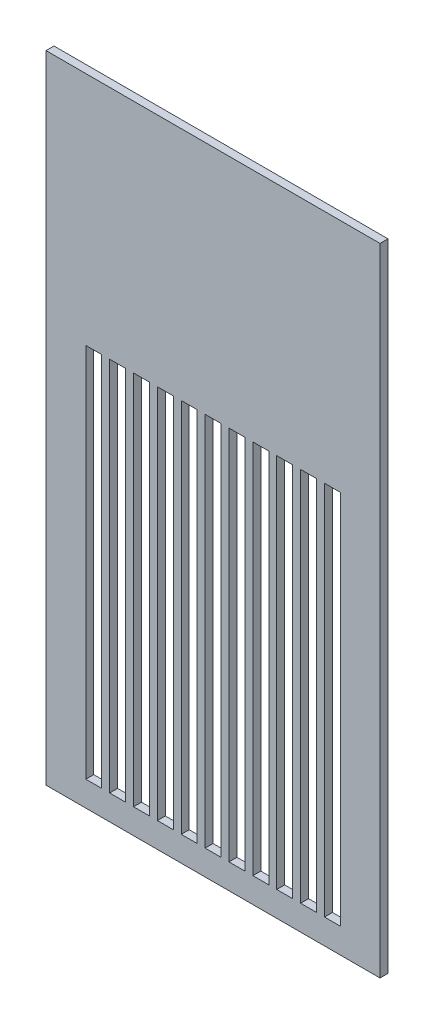
SolidWorks part; units mm, degrees
ref_plane "Front Plane" through (0, 0, 0) normal (0, 0, 1) x (1, 0, 0)
ref_plane "Top Plane" through (0, 0, 0) normal (0, 1, 0) x (1, 0, 0)
ref_plane "Right Plane" through (0, 0, 0) normal (1, 0, 0) x (0, 0, -1)
sketch "Sketch1" plane through (0, 0, 0) normal (0, 0, 1) x (1, 0, 0)
  line L0 (0, 0) -> (133.35, 0)
  line L1 (133.35, 0) -> (133.35, 254)
  line L2 (133.35, 254) -> (0, 254)
  line L3 (0, 254) -> (0, 0)
  dimension "D1" = 133.35
  dimension "D2" = 254
extrude "Boss-Extrude1" add sketch "Sketch1" along normal blind 3.175
sketch "Sketch2" plane through (0, 0, 3.175) normal (0, 0, 1) x (1, 0, 0)
  line L0 (15.875, 160) -> (15.875, 10)
  line L1 (15.875, 10) -> (22.225, 10)
  line L2 (22.225, 10) -> (22.225, 160)
  line L3 (22.225, 160) -> (15.875, 160)
  line L4 (0, 254) -> (0, 0) construction
  line L5 (0, 0) -> (133.35, 0) construction
  line L6 (31.755, 160) -> (25.405, 160)
  line L7 (25.405, 160) -> (25.405, 10)
  line L8 (25.405, 10) -> (31.755, 10)
  line L9 (31.755, 10) -> (31.755, 160)
  line L10 (41.285, 160) -> (34.935, 160)
  line L11 (34.935, 160) -> (34.935, 10)
  line L12 (34.935, 10) -> (41.285, 10)
  line L13 (41.285, 10) -> (41.285, 160)
  line L14 (50.815, 160) -> (44.465, 160)
  line L15 (44.465, 160) -> (44.465, 10)
  line L16 (44.465, 10) -> (50.815, 10)
  line L17 (50.815, 10) -> (50.815, 160)
  line L18 (60.345, 160) -> (53.995, 160)
  line L19 (53.995, 160) -> (53.995, 10)
  line L20 (53.995, 10) -> (60.345, 10)
  line L21 (60.345, 10) -> (60.345, 160)
  line L22 (69.875, 160) -> (63.525, 160)
  line L23 (63.525, 160) -> (63.525, 10)
  line L24 (63.525, 10) -> (69.875, 10)
  line L25 (69.875, 10) -> (69.875, 160)
  line L26 (79.405, 160) -> (73.055, 160)
  line L27 (73.055, 160) -> (73.055, 10)
  line L28 (73.055, 10) -> (79.405, 10)
  line L29 (79.405, 10) -> (79.405, 160)
  line L30 (88.935, 160) -> (82.585, 160)
  line L31 (82.585, 160) -> (82.585, 10)
  line L32 (82.585, 10) -> (88.935, 10)
  line L33 (88.935, 10) -> (88.935, 160)
  line L34 (98.465, 160) -> (92.115, 160)
  line L35 (92.115, 160) -> (92.115, 10)
  line L36 (92.115, 10) -> (98.465, 10)
  line L37 (98.465, 10) -> (98.465, 160)
  line L38 (107.995, 160) -> (101.645, 160)
  line L39 (101.645, 160) -> (101.645, 10)
  line L40 (101.645, 10) -> (107.995, 10)
  line L41 (107.995, 10) -> (107.995, 160)
  line L42 (117.525, 160) -> (111.175, 160)
  line L43 (111.175, 160) -> (111.175, 10)
  line L44 (111.175, 10) -> (117.525, 10)
  line L45 (117.525, 10) -> (117.525, 160)
  line L46 (22.225, 160) -> (31.755, 160) construction
  dimension "D1" = 150
  dimension "D2" = 6.35
  dimension "D3" = 15.875
  dimension "D4" = 10
  dimension "D6" = 9.53
  dimension "D5" = 11
extrude "Cut-Extrude1" cut sketch "Sketch2" against normal up to surface (3.175 mm away) up to face at (66.675, 127, 0)
equation "\"bottomThickness\"= .220in"
equation "\"wallThickness\"= .125in"
equation "\"D1@Boss-Extrude1\"=\"wallThickness\""
